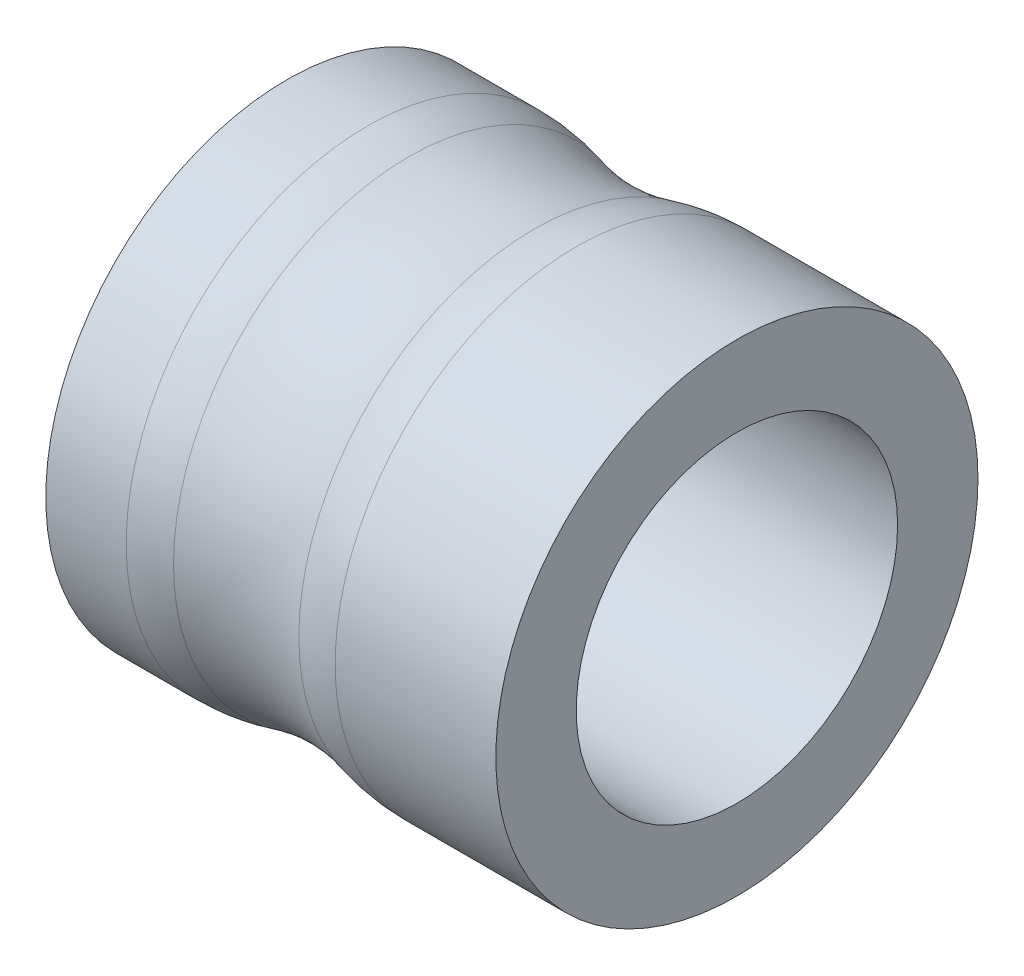
SolidWorks part; units mm, degrees
material "Rubber"
ref_plane "Front Plane" through (0, 0, 0) normal (0, 0, 1) x (1, 0, 0)
ref_plane "Top Plane" through (0, 0, 0) normal (0, 1, 0) x (1, 0, 0)
ref_plane "Right Plane" through (0, 0, 0) normal (1, 0, 0) x (0, 0, -1)
sketch "Sketch1" plane through (0, 0, 0) normal (0, 0, 1) x (1, 0, 0)
  line L0 (0, 0) -> (5.6, 0) construction
  line L1 (0, 2) -> (5.6, 2)
  line L2 (0, 2) -> (0, 3)
  line L3 (0, 3) -> (1, 3)
  line L4 (5.6, 2) -> (5.6, 3)
  line L5 (3.6, 3) -> (5.6, 3)
  arc A0 (1.52, 2.9312) -> (3.08, 2.9312) centre (2.3, 5.828) ccw
  arc A1 (1.52, 2.9312) -> (1, 3) centre (1, 1) ccw
  arc A2 (3.6, 3) -> (3.08, 2.9312) centre (3.6, 1) ccw
  point P14 (3.3011, 3)
  dimension "D4" = 2
  dimension "D7" = 3
  dimension "D1" = 5.6
  dimension "D2" = 4
  dimension "D3" = 6
  dimension "D5" = 1
  dimension "D6" = 2
ref_axis "Axis1" through (5.88, 0, 0) along (-1, 0, 0)
revolve "Revolve1" add sketch "Sketch1" angle 360 about axis through (5.88, 0, 0) along (-1, 0, 0)
